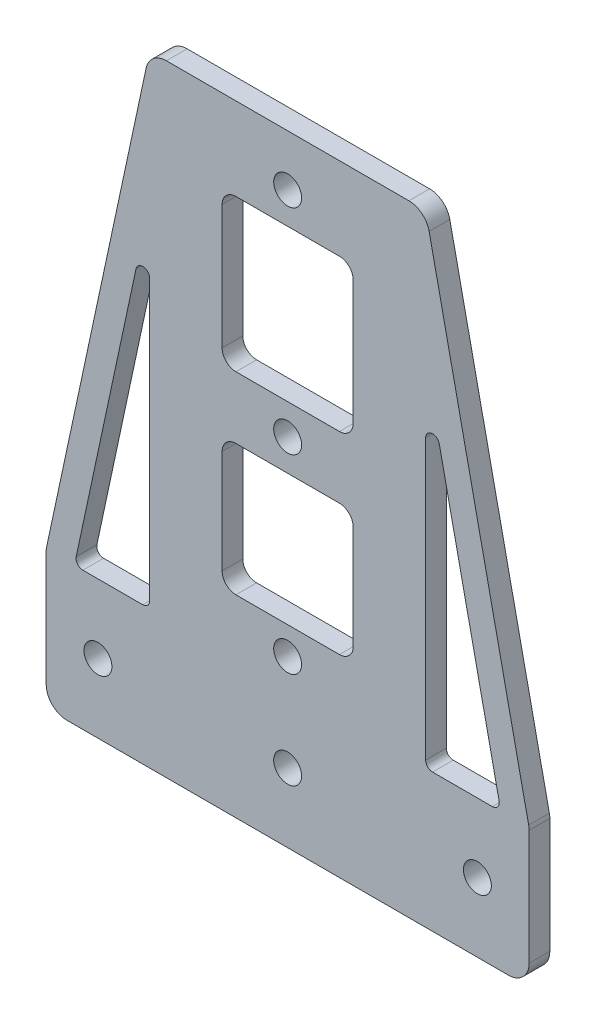
SolidWorks part; units mm, degrees
material "Thornel Mat VMA"
ref_plane "前视基准面" through (0, 0, 0) normal (0, 0, 1) x (1, 0, 0)
ref_plane "上视基准面" through (0, 0, 0) normal (0, 1, 0) x (1, 0, 0)
ref_plane "右视基准面" through (0, 0, 0) normal (1, 0, 0) x (0, 0, -1)
other "Configuration Table"
sketch "草图1" plane through (0, 0, 0) normal (0, 0, 1) x (1, 0, 0)
  line L0 (0, 0) -> (-70, 0)
  line L1 (-70, 0) -> (-70, 20)
  line L2 (-70, 20) -> (-55, 90)
  line L3 (-55, 90) -> (-15, 90)
  line L4 (-15, 90) -> (0, 20)
  line L5 (0, 20) -> (0, 0)
  point P8 (-35, 90)
  point P9 (-35, 0)
  dimension "D1" = 40
  dimension "D2" = 70
  dimension "D3" = 90
  dimension "D4" = 20
extrude "凸台-拉伸1" add sketch "草图1" along normal blind 3
sketch "草图3" plane through (0, 0, 3) normal (0, 0, 1) x (1, 0, 0)
  line L0 (-35, 90) -> (-35, 0) construction
  line L1 (-44.5, 56) -> (-25.5, 56)
  line L2 (-44.5, 56) -> (-44.5, 78)
  line L3 (-44.5, 78) -> (-25.5, 78)
  line L4 (-25.5, 56) -> (-25.5, 78)
  line L5 (-44.5, 56) -> (-25.5, 78) construction
  line L6 (-44.5, 78) -> (-25.5, 56) construction
  line L7 (-44.5, 28) -> (-25.5, 28)
  line L8 (-44.5, 28) -> (-44.5, 47)
  line L9 (-44.5, 47) -> (-25.5, 47)
  line L10 (-25.5, 28) -> (-25.5, 47)
  line L11 (-44.5, 28) -> (-25.5, 47) construction
  line L12 (-44.5, 47) -> (-25.5, 28) construction
  line L13 (-15, 90) -> (-55, 90) construction
  line L14 (-70, 0) -> (0, 0) construction
  line L15 (-55, 70.9096) -> (-55, 20)
  line L16 (-55, 20) -> (-65.9092, 20)
  line L17 (-65.9092, 20) -> (-55, 70.9096)
  line L18 (-55, 90) -> (-70, 20) construction
  line L19 (-4.0908, 20) -> (-15, 70.9096)
  line L20 (-15, 20) -> (-4.0908, 20)
  line L21 (-15, 70.9096) -> (-15, 20)
  point P0 (-35, 67)
  point P5 (-35, 37.5)
  dimension "D1" = 19
  dimension "D2" = 28
  dimension "D3" = 4
  dimension "D4" = 40
  dimension "D5" = 12
  dimension "D6" = 22
extrude "切除-拉伸1" cut sketch "草图3" against normal blind 3
fillet "圆角1" radius 1 6 edges at (-15, 70.9096, 1.5) (-4.0908, 20, 1.5) (-15, 20, 1.5) (-55, 70.9096, 1.5) (-65.9092, 20, 1.5) (-55, 20, 1.5)
fillet "圆角2" radius 2 8 edges at (-25.5, 56, 1.5) (-44.5, 56, 1.5) (-44.5, 78, 1.5) (-25.5, 78, 1.5) (-25.5, 28, 1.5) (-44.5, 47, 1.5) (-25.5, 47, 1.5) (-44.5, 28, 1.5)
fillet "圆角3" radius 3 6 edges at (0, 0, 1.5) (-70, 0, 1.5) (-70, 20, 1.5) (0, 20, 1.5) (-15, 90, 1.5) (-55, 90, 1.5)
sketch "草图4" plane through (0, 0, 3) normal (0, 0, 1) x (1, 0, 0)
  line L0 (-67, 0) -> (-3, 0) construction
  line L1 (-35, 28) -> (-35, 10) construction
  line L2 (-42.5, 28) -> (-27.5, 28) construction
  circle A0 centre (-62.5, 10) radius 2.025
  circle A1 centre (-35, 10) radius 2.025
  circle A2 centre (-7.5, 10) radius 2.025
  dimension "D2" = 4.05
  dimension "D3" = 55
  dimension "D1" = 10
extrude "切除-拉伸2" cut sketch "草图4" against normal blind 3
sketch "草图5" plane through (0, 0, 0) normal (0, 0, -1) x (-1, 0, 0)
  circle A0 centre (35, 82.567) radius 2.025
  circle A1 centre (35, 51.567) radius 2.025
  circle A2 centre (35, 24) radius 2.025
  circle A3 centre (35, 82.567) radius 2.025 construction
  circle A4 centre (35, 51.567) radius 2.025 construction
  circle A5 centre (35, 24) radius 2.025 construction
  dimension "D1" = 4.05
extrude "切除-拉伸3" cut sketch "草图5" against normal blind 10
